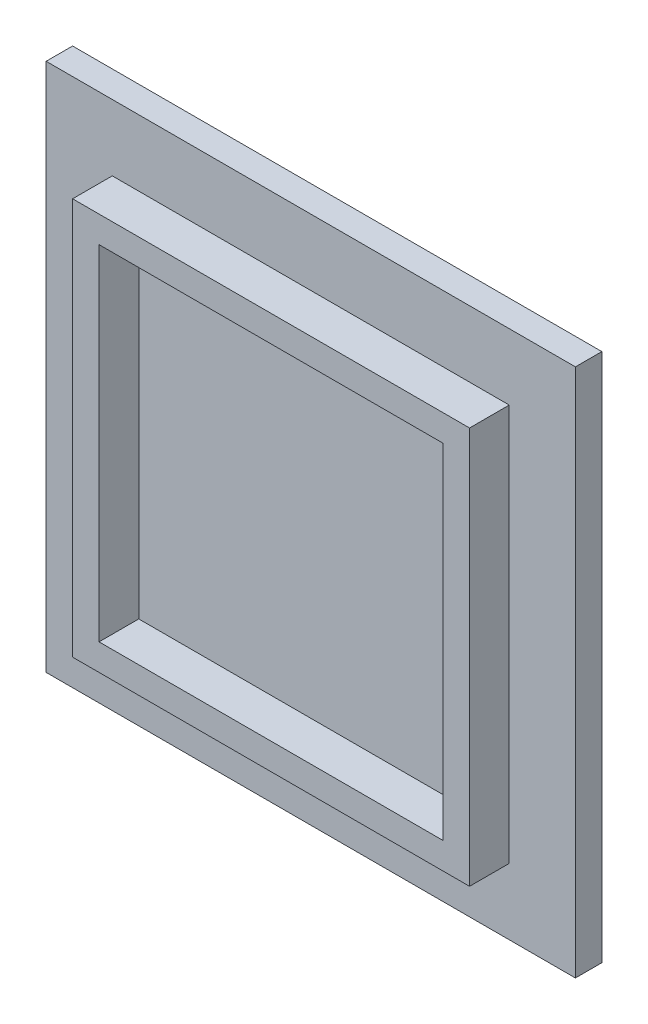
SolidWorks part; units mm, degrees
ref_plane "Front Plane" through (0, 0, 0) normal (0, 0, 1) x (1, 0, 0)
ref_plane "Top Plane" through (0, 0, 0) normal (0, 1, 0) x (1, 0, 0)
ref_plane "Right Plane" through (0, 0, 0) normal (1, 0, 0) x (0, 0, -1)
sketch "Sketch1" plane through (0, 0, 0) normal (0, 0, 1) x (1, 0, 0)
  line L1 (-25.1923, 15.1442) -> (14.8077, 15.1442)
  line L2 (-25.1923, 15.1442) -> (-25.1923, -24.8558)
  line L3 (-25.1923, -24.8558) -> (14.8077, -24.8558)
  line L4 (14.8077, 15.1442) -> (14.8077, -24.8558)
  dimension "D1" = 40
  dimension "D2" = 40
extrude "Boss-Extrude1" add sketch "Sketch1" along normal blind 2
sketch "Sketch2" plane through (0, 0, 2) normal (0, 0, 1) x (1, 0, 0)
  line L0 (-25.1923, 15.1442) -> (14.8077, -24.8558) construction
  line L1 (-25.1923, -24.8558) -> (14.8077, 15.1442) construction
  line L3 (9.8077, -19.8558) -> (-20.1923, -19.8558)
  line L4 (9.8077, -19.8558) -> (9.8077, 10.1442)
  line L5 (9.8077, 10.1442) -> (-20.1923, 10.1442)
  line L6 (-20.1923, -19.8558) -> (-20.1923, 10.1442)
  line L7 (9.8077, -19.8558) -> (-20.1923, 10.1442) construction
  line L8 (9.8077, 10.1442) -> (-20.1923, -19.8558) construction
  line L9 (7.8077, -17.8558) -> (-18.1923, -17.8558)
  line L10 (7.8077, -17.8558) -> (7.8077, 8.1442)
  line L11 (7.8077, 8.1442) -> (-18.1923, 8.1442)
  line L12 (-18.1923, -17.8558) -> (-18.1923, 8.1442)
  line L13 (7.8077, -17.8558) -> (-18.1923, 8.1442) construction
  line L14 (7.8077, 8.1442) -> (-18.1923, -17.8558) construction
  point P8 (-5.1923, -4.8558)
  point P9 (-5.1923, -4.8558)
  point P14 (-5.1923, -4.8558)
  point P19 (-17.1042, 7.0561)
  point P20 (7.9916, 8.3281)
  point P21 (8.448, 8.7845)
  point P22 (-36.0435, 17.8046)
  point P23 (0, 0)
  point P24 (6.4076, 6.7442)
  point P25 (7.7955, 8.1321)
  dimension "D1" = 30
  dimension "D2" = 26
extrude "Boss-Extrude2" add sketch "Sketch2" along normal blind 3
